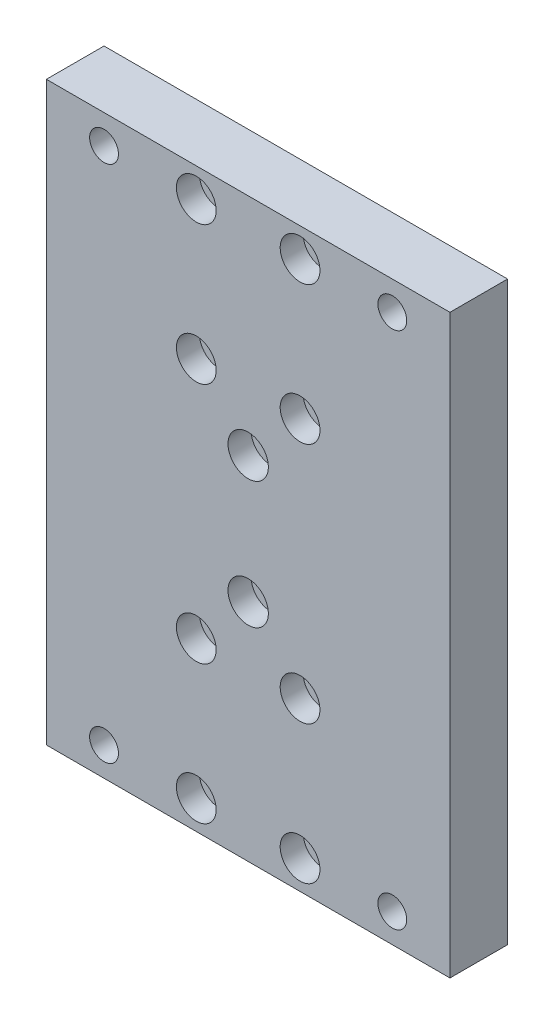
SolidWorks part; units mm, degrees
ref_plane "Front Plane" through (0, 0, 0) normal (0, 0, 1) x (1, 0, 0)
ref_plane "Top Plane" through (0, 0, 0) normal (0, 1, 0) x (1, 0, 0)
ref_plane "Right Plane" through (0, 0, 0) normal (1, 0, 0) x (0, 0, -1)
sketch "Sketch1" plane through (0, 0, 0) normal (0, 0, 1) x (1, 0, 0)
  line L1 (35, -50) -> (-35, -50)
  line L2 (35, -50) -> (35, 50)
  line L3 (35, 50) -> (-35, 50)
  line L4 (-35, -50) -> (-35, 50)
  line L5 (35, -50) -> (-35, 50) construction
  line L6 (35, 50) -> (-35, -50) construction
  point P0 (0, 0)
  dimension "D1" = 70
  dimension "D2" = 100
extrude "Boss-Extrude1" add sketch "Sketch1" along normal blind 10
sketch "Sketch2" plane through (0, 0, 0) normal (0, 0, -1) x (-1, 0, 0)
  line L0 (0, 50) -> (0, 0) construction
  line L1 (-35, 50) -> (35, 50) construction
  line L2 (0, 0) -> (-35, 0) construction
  line L3 (-35, -50) -> (-35, 50) construction
  circle A0 centre (-25, 45) radius 2.5
  circle A1 centre (25, 45) radius 2.5
  circle A2 centre (-25, -45) radius 2.5
  circle A3 centre (25, -45) radius 2.5
  dimension "D1" = 5
  dimension "D2" = 5
  dimension "D3" = 10
extrude "Cut-Extrude1" cut sketch "Sketch2" against normal through all
sketch "Sketch3" plane through (0, 0, 0) normal (0, 0, -1) x (-1, 0, 0)
  circle A1 centre (9, 21) radius 1.5
  circle A2 centre (9, 21) radius 1.5
  circle A3 centre (9, 45) radius 1.5
  circle A4 centre (9, 45) radius 1.5
  circle A5 centre (-9, 21) radius 1.5
  circle A6 centre (-9, 21) radius 1.5
  circle A7 centre (-9, 45) radius 1.5
  circle A8 centre (-9, 45) radius 1.5
  circle A9 centre (9, -45) radius 1.5
  circle A10 centre (9, -45) radius 1.5
  circle A11 centre (9, -21) radius 1.5
  circle A12 centre (9, -21) radius 1.5
  circle A13 centre (-9, -45) radius 1.5
  circle A14 centre (-9, -45) radius 1.5
  circle A15 centre (-9, -21) radius 1.5
  circle A16 centre (-9, -21) radius 1.5
  dimension "D1" = 0
  dimension "D2" = 0
  dimension "D3" = 0
  dimension "D4" = 0
  dimension "D5" = 0
  dimension "D6" = 0
  dimension "D7" = 0
  dimension "D8" = 0
extrude "Cut-Extrude2" cut sketch "Sketch3" against normal through all
sketch "Sketch4" plane through (0, 0, 10) normal (0, 0, 1) x (1, 0, 0)
  line L0 (0, 50) -> (0, 0) construction
  line L1 (35, 50) -> (-35, 50) construction
  line L2 (0, 0) -> (-35, 0) construction
  line L3 (-35, 50) -> (-35, -50) construction
  line L4 (0, 33) -> (-35, 33) construction
  circle A0 centre (-9, 45) radius 3.45
  circle A1 centre (-9, 21) radius 3.45
  circle A2 centre (9, 21) radius 3.45
  circle A3 centre (9, 45) radius 3.45
  circle A4 centre (9, -21) radius 3.45
  circle A5 centre (-9, -21) radius 3.45
  circle A6 centre (-9, -45) radius 3.45
  circle A7 centre (9, -45) radius 3.45
  dimension "D1" = 6.9
extrude "Cut-Extrude3" cut sketch "Sketch4" against normal blind 4
sketch "Sketch5" plane through (0, 0, 10) normal (0, 0, 1) x (1, 0, 0)
  circle A1 centre (0, -11) radius 2
  circle A2 centre (0, -11) radius 2
  circle A3 centre (0, 11) radius 2
  circle A4 centre (0, 11) radius 2
  dimension "D1" = 0
  dimension "D2" = 0
extrude "Cut-Extrude4" cut sketch "Sketch5" against normal through all
sketch "Sketch6" plane through (0, 0, 10) normal (0, 0, 1) x (1, 0, 0)
  circle A0 centre (0, 11) radius 3.5
  circle A1 centre (0, -11) radius 3.5
  dimension "D1" = 7
extrude "Cut-Extrude5" cut sketch "Sketch6" against normal blind 4
